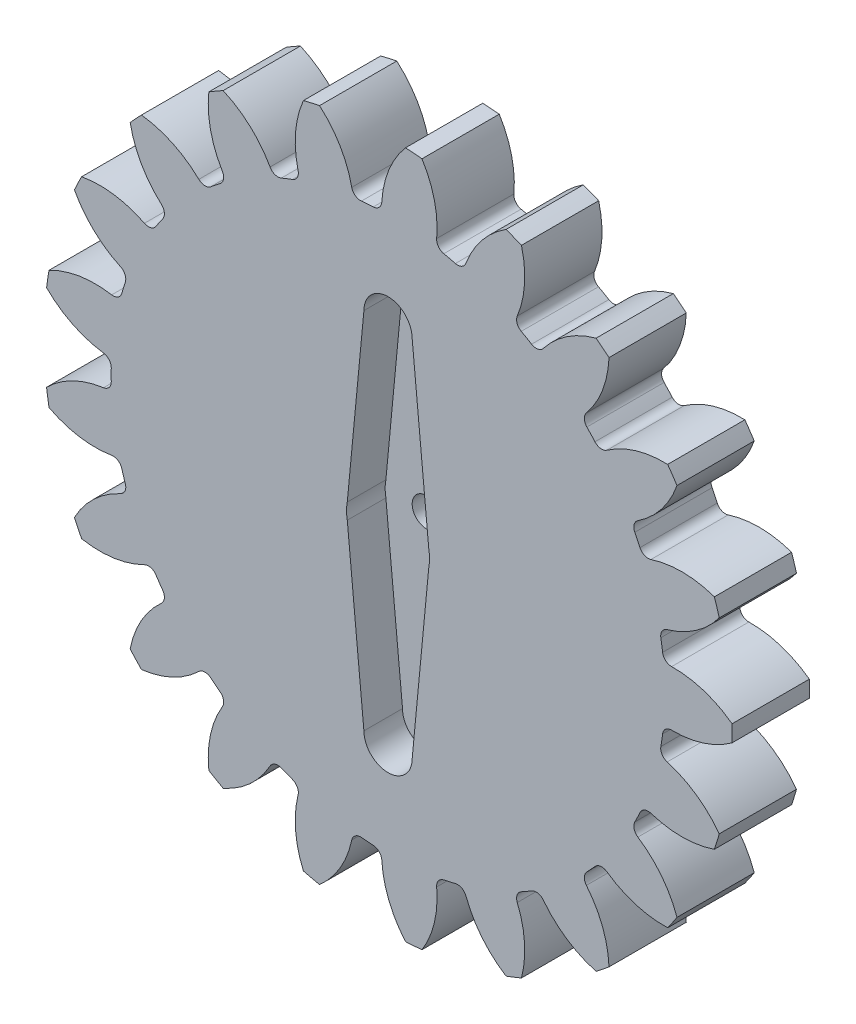
SolidWorks part; units mm, degrees
ref_plane "Front Plane" through (0, 0, 0) normal (0, 0, 1) x (1, 0, 0)
ref_plane "Top Plane" through (0, 0, 0) normal (0, 1, 0) x (1, 0, 0)
ref_plane "Right Plane" through (0, 0, 0) normal (1, 0, 0) x (0, 0, -1)
sketch "Sketch1" plane through (0, 0, 0) normal (0, 0, 1) x (1, 0, 0)
  circle A0 centre (0, 0) radius 32.55
  circle A1 centre (0, 0) radius 35.65
  circle A2 centre (0, 0) radius 28.675
  dimension "D1" = 65.1
  dimension "D2" = 71.3
  dimension "D3" = 6.975
extrude "Boss-Extrude1" add sketch "Sketch1" along normal mid plane 8 contours A1
sketch "Sketch4" plane through (0, 0, 0) normal (0, 0, 1) x (1, 0, 0)
  line L0 (0, 0) -> (-35.65, 0) construction
  line L1 (-32.459, -2.4325) -> (-32.459, 2.4325) construction
  line L2 (0, 0) -> (-28.6367, -1.4809) construction
  line L3 (-27.2425, 0) -> (-36.4004, -4.2704) construction
  line L4 (0, 0) -> (-35.2518, 5.3134) construction
  line L5 (-32.459, 2.4325) -> (-31.7339, 7.2431) construction
  circle A0 centre (0, 0) radius 35.65 construction
  arc A1 (-36.2424, -5.451) -> (-28.6367, -1.4809) centre (-28.1046, -11.7704) cw
  arc A2 (-36.2424, 5.451) -> (-28.6367, 1.4809) centre (-28.1046, 11.7704) ccw
  arc A3 (-36.2424, 5.451) -> (-36.2424, -5.451) centre (0, 0) ccw
  circle A4 centre (0, 0) radius 28.675
  arc A5 (-28.6367, 1.4809) -> (-28.6367, -1.4809) centre (0, 0) ccw
  circle A6 centre (0, 0) radius 35.65
  arc A7 (-35.3694, -4.4642) -> (-35.3694, 4.4642) centre (0, 0) ccw
  circle A10 centre (0, 0) radius 36.65 construction
  circle A11 centre (0, 0) radius 35.65 construction
  circle A15 centre (0, 0) radius 32.55
  circle A16 centre (0, 0) radius 32.55
  point P20 (32.9925, 10.0868)
  point P22 (35.5, 0)
  dimension "D4" = 25
  dimension "D5" = 8.571
  dimension "D2" = 0
  dimension "D3" = 1
  dimension "D6" = 0
extrude "Cut-Extrude1" cut sketch "Sketch4" against normal through all both and the other way through all contours A16 A2 A3 A1 | A2 A16 A1 A5
fillet "Fillet1" radius 0.93 2 edges at (-28.6367, -1.4809, 0) (-28.6367, 1.4809, 0)
pattern_circular "CirPattern1" count 21 over 360 about axis through (0, 0, 0) along (0, 0, 1) of "Cut-Extrude1", "Fillet1"
sketch "Sketch5" plane through (0, 0, 4) normal (0, 0, 1) x (1, 0, 0)
  line L0 (0, 0) -> (0, 21.35) construction
  line L1 (-2.5, 18.85) -> (-4.2223, 0.8138)
  line L2 (2.5, 18.85) -> (4.2223, 0.8138)
  line L3 (-4.3, 0) -> (4.3, 0) construction
  line L4 (2.5, -18.85) -> (4.2223, -0.8138)
  line L5 (-2.5, -18.85) -> (-4.2223, -0.8138)
  arc A0 (-4.2223, 0.8138) -> (-4.2223, -0.8138) centre (0, 0) ccw
  arc A1 (2.5, 18.85) -> (-2.5, 18.85) centre (0, 18.85) ccw
  arc A2 (2.5, -18.85) -> (-2.5, -18.85) centre (0, -18.85) cw
  arc A3 (4.2223, -0.8138) -> (4.2223, 0.8138) centre (0, 0) ccw
  dimension "D1" = 8.6
  dimension "D3" = 5
  dimension "D2" = 21.35
extrude "Cut-Extrude3" cut sketch "Sketch5" against normal blind 4
sketch "Sketch6" plane through (0, 0, 0) normal (0, 0, 1) x (1, 0, 0)
  circle A0 centre (0, 0) radius 1.5
  dimension "D1" = 3
extrude "Cut-Extrude4" cut sketch "Sketch6" against normal through all both and the other way through all
equation "\"Module\"= 3.1mm"
equation "\"Number of Teeth\"= 21"
equation "\"D1@Sketch1\"=\"Module\" * \"Number of Teeth\""
equation "\"D2@Sketch1\"=(\"Number of Teeth\" + 2) * \"Module\""
equation "\"D3@Sketch1\"=\"Module\" * if(\"Module\"=>1.25,2.25,2.4)"
equation "\"D5@Sketch4\"=180 / \"Number of Teeth\""
equation "\"D1@Fillet1\"=.3 * \"Module\""
equation "\"D1@CirPattern1\"=\"Number of Teeth\""
